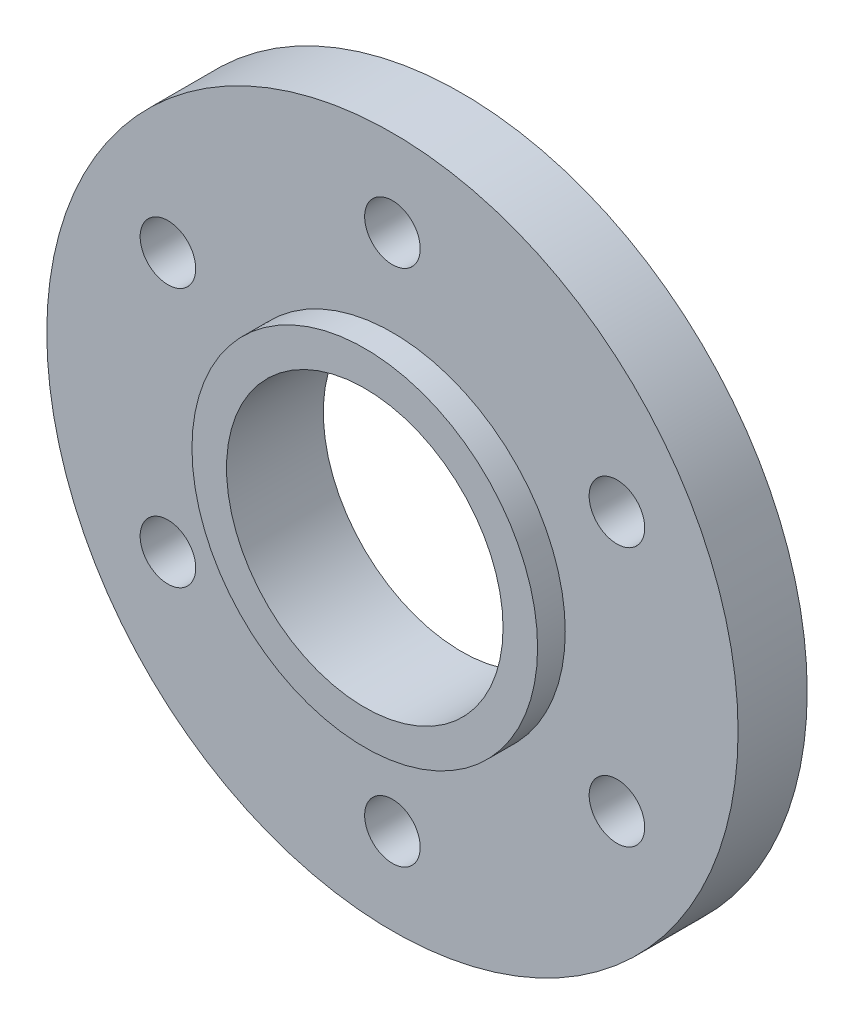
SolidWorks part; units mm, degrees
ref_plane "Front Plane" through (0, 0, 0) normal (0, 0, 1) x (1, 0, 0)
ref_plane "Top Plane" through (0, 0, 0) normal (0, 1, 0) x (1, 0, 0)
ref_plane "Right Plane" through (0, 0, 0) normal (1, 0, 0) x (0, 0, -1)
sketch "Sketch1" plane through (0, 0, 0) normal (0, 0, 1) x (1, 0, 0)
  circle A0 centre (0, 0) radius 31.75
  dimension "D1" = 63.5
extrude "Boss-Extrude1" add sketch "Sketch1" along normal blind 6.35
sketch "Sketch2" plane through (0, 0, 6.35) normal (0, 0, 1) x (1, 0, 0)
  circle A0 centre (0, 0) radius 12.7
  circle A1 centre (0, 0) radius 23.8125 construction
  circle A2 centre (0, 23.8125) radius 2.5527
  circle A3 centre (20.6222, 11.9063) radius 2.5527
  circle A4 centre (20.6222, -11.9062) radius 2.5527
  circle A5 centre (0, -23.8125) radius 2.5527
  circle A6 centre (-20.6222, -11.9063) radius 2.5527
  circle A7 centre (-20.6222, 11.9062) radius 2.5527
  point P19 (0, 0)
  dimension "D1" = 25.4
  dimension "D2" = 47.625
  dimension "D3" = 5.1054
  dimension "D4" = 6
extrude "Cut-Extrude1" cut sketch "Sketch2" against normal through all
sketch "Sketch3" plane through (0, 0, 6.35) normal (0, 0, 1) x (1, 0, 0)
  circle A0 centre (0, 0) radius 12.7
  circle A1 centre (0, 0) radius 15.875
  dimension "D1" = 31.75
  dimension "D2" = 25.4
extrude "Boss-Extrude2" add sketch "Sketch3" along normal blind 2.54
